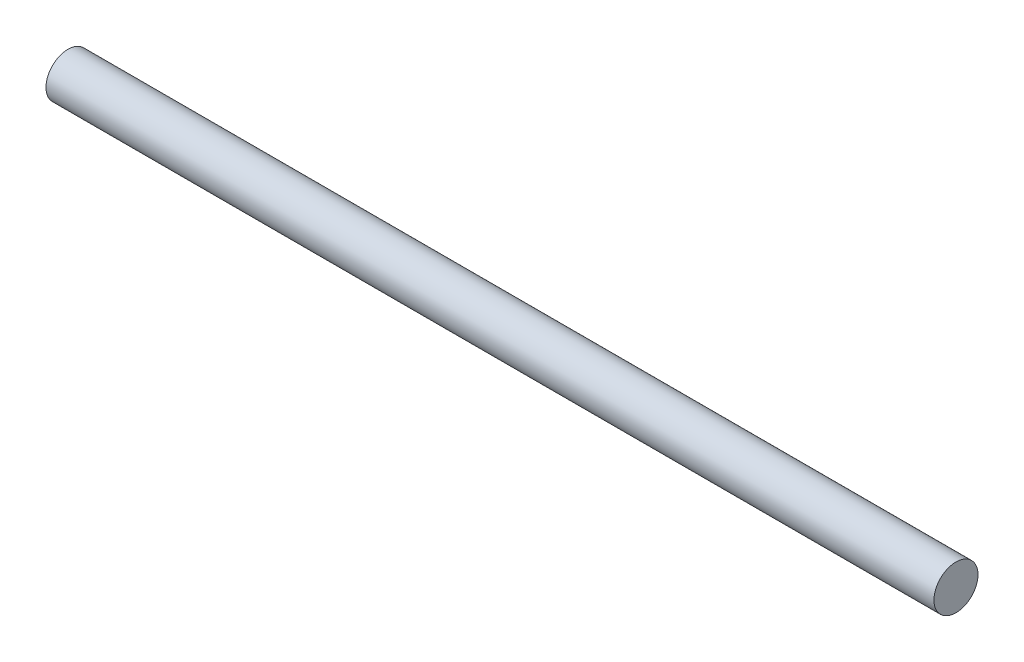
SolidWorks part; units mm, degrees
material "6061 Alloy"
ref_plane "Front Plane" through (0, 0, 0) normal (0, 0, 1) x (1, 0, 0)
ref_plane "Top Plane" through (0, 0, 0) normal (0, 1, 0) x (1, 0, 0)
ref_plane "Right Plane" through (0, 0, 0) normal (1, 0, 0) x (0, 0, -1)
sketch "Sketch1" plane through (0, 0, 0) normal (1, 0, 0) x (0, 0, -1)
  circle A0 centre (0, 0) radius 1.5875
  dimension "D1" = 3.175
extrude "Boss-Extrude1" add sketch "Sketch1" along normal mid plane 64
